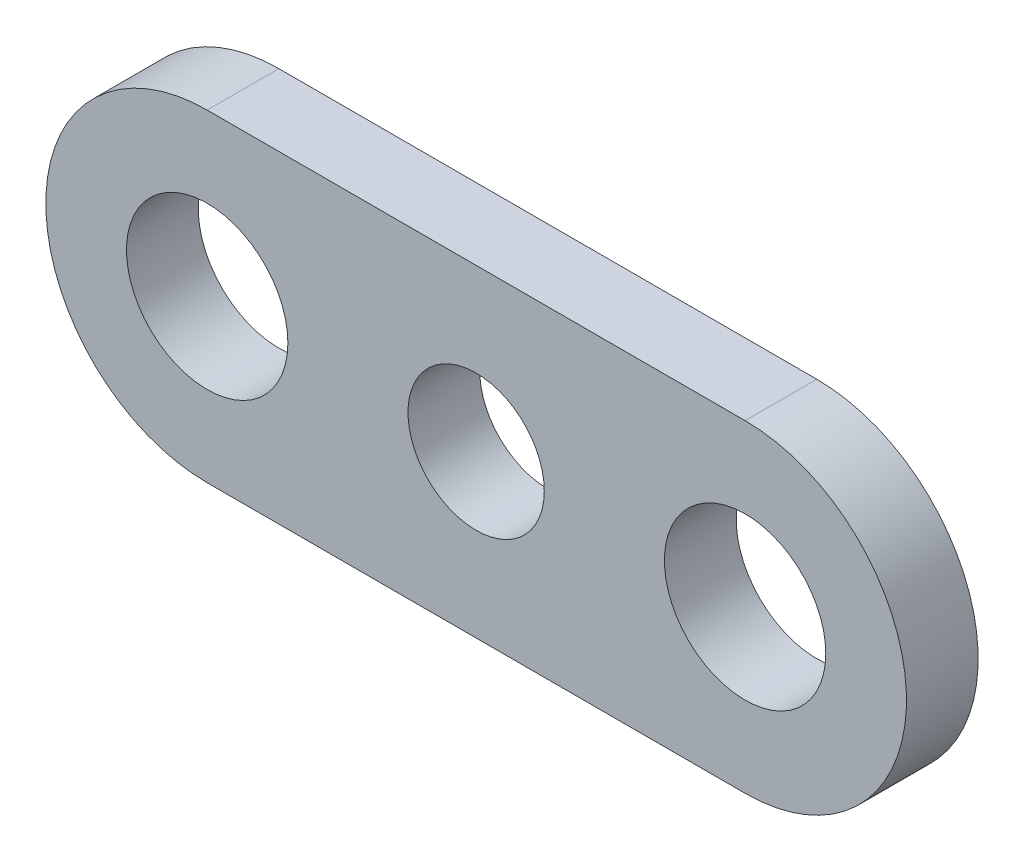
SolidWorks part; units mm, degrees
material "3.3315 (EN-AW 5005)"
ref_plane "Front Plane" through (0, 0, 0) normal (0, 0, 1) x (1, 0, 0)
ref_plane "Top Plane" through (0, 0, 0) normal (0, 1, 0) x (1, 0, 0)
ref_plane "Right Plane" through (0, 0, 0) normal (1, 0, 0) x (0, 0, -1)
sketch "Sketch1" plane through (0, 0, 0) normal (0, 0, 1) x (1, 0, 0)
  line L0 (-7.5, 0) -> (7.5, 0) construction
  line L1 (-7.5, 4.5) -> (7.5, 4.5)
  line L2 (-7.5, -4.5) -> (7.5, -4.5)
  circle A0 centre (0, 0) radius 1.9
  arc A1 (-7.5, 4.5) -> (-7.5, -4.5) centre (-7.5, 0) ccw
  arc A2 (7.5, -4.5) -> (7.5, 4.5) centre (7.5, 0) ccw
  point P5 (0, 0)
  dimension "D1" = 3.8
  dimension "D2" = 15
  dimension "D3" = 9
extrude "Boss-Extrude1" add sketch "Sketch1" along normal blind 2
hole_wizard "M4 Clearance Hole1" positions "Sketch2" profile "Sketch3" hole size "M4" standard "ISO" end condition through all
sketch "Sketch2" plane through (0, 0, 2) normal (0, 0, 1) x (1, 0, 0)
  point P0 (-7.5, 0)
  point P3 (7.5, 0)
sketch "Sketch3" plane through (-7.5, 0, 2) normal (1, 0, 0) x (0, -1, 0)
  line L0 (0, 0) -> (0, 2)
  line L1 (0, 2) -> (2.25, 2)
  line L2 (2.25, 2) -> (2.25, 0)
  line L5 (2.25, 0) -> (0, 0)
  line L11 (0, -6.35) -> (0, 107.95) construction
  dimension "Thru Hole Dia." = 4.5
  dimension "Thru Hole Depth" = 2
